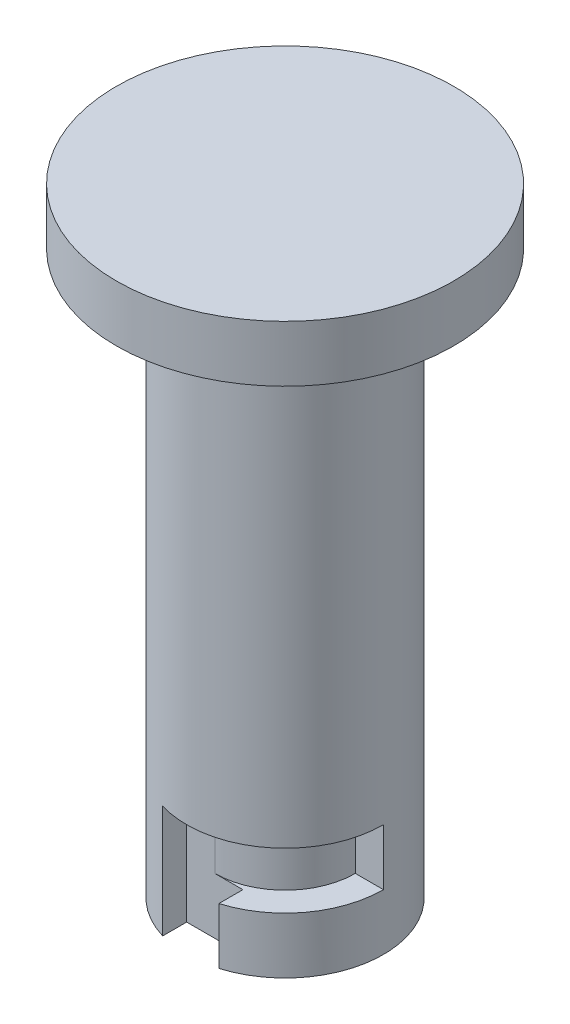
SolidWorks part; units mm, degrees
ref_plane "Front Plane" through (0, 0, 0) normal (0, 0, 1) x (1, 0, 0)
ref_plane "Top Plane" through (0, 0, 0) normal (0, 1, 0) x (1, 0, 0)
ref_plane "Right Plane" through (0, 0, 0) normal (1, 0, 0) x (0, 0, -1)
sketch "Sketch1" plane through (0, 0, 0) normal (0, 1, 0) x (1, 0, 0)
  circle A0 centre (0, 0) radius 3.5
  dimension "D1" = 7
extrude "Boss-Extrude1" add sketch "Sketch1" along normal blind 20
sketch "Sketch2" plane through (0, 20, 0) normal (0, 1, 0) x (1, 0, 0)
  circle A0 centre (0, 0) radius 6
extrude "Boss-Extrude2" add sketch "Sketch2" along normal blind 2
sketch "Sketch3" plane through (0, 0, 0) normal (0, -1, 0) x (1, 0, 0)
  line L0 (0, 3.875) -> (0, -49996.125) construction
  line L1 (0, 3.5) -> (-1, 3.5)
  line L2 (-1, 3.5) -> (-1, 2.5)
  line L3 (-1, 2.5) -> (1, 2.5)
  line L4 (1, 2.5) -> (1, 3.5)
  line L5 (1, 3.5) -> (0, 3.5)
  line L6 (0, 0) -> (-50000, 0) construction
  line L7 (-1, -3.5) -> (-1, -2.5)
  line L8 (-1, -2.5) -> (1, -2.5)
  line L9 (1, -2.5) -> (1, -3.5)
  line L10 (1, -3.5) -> (0, -3.5)
  line L11 (0, -3.5) -> (-1, -3.5)
  circle A2 centre (0, 0) radius 3.5 construction
  dimension "D1" = 1
  dimension "D2" = 2
  dimension "D3" = 1
extrude "Cut-Extrude1" cut sketch "Sketch3" against normal blind 4
sketch "Sketch6" plane through (0, 0, 0) normal (1, 0, 0) x (0, 0, -1)
  line L0 (2.5, 2) -> (3.5, 2)
  line L5 (0, 0) -> (0, 22) construction
  line L6 (-3.3541, 0) -> (3.3541, 0) construction
  line L7 (6, 22) -> (-6, 22) construction
  line L8 (-2.5, 4) -> (-3.5, 4)
  line L9 (-2.5, 4) -> (-2.5, 2)
  line L10 (-2.5, 2) -> (-3.5, 2)
  line L11 (-3.5, 4) -> (-3.5, 2)
  line L16 (3.5, 4) -> (3.5, 2)
  line L17 (2.5, 4) -> (3.5, 4)
  line L18 (2.5, 4) -> (2.5, 2)
  dimension "D1" = 2
  dimension "D2" = 1
revolve "Cut-Revolve1" cut sketch "Sketch6" angle 90 about L5
